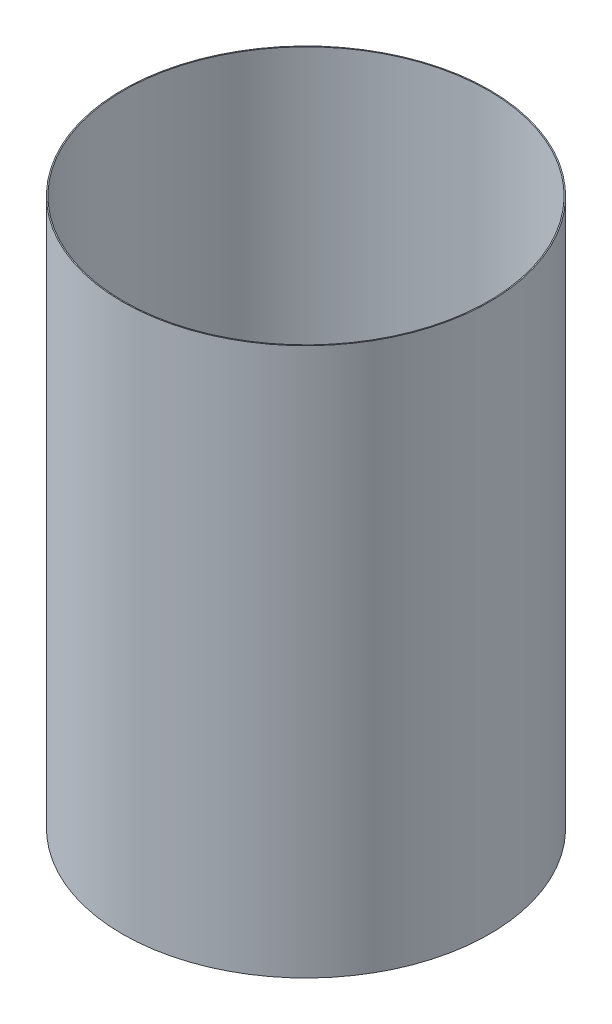
SolidWorks part; units mm, degrees
material "Thornel Mat VMA"
ref_plane "Front Plane" through (0, 0, 0) normal (0, 0, 1) x (1, 0, 0)
ref_plane "Top Plane" through (0, 0, 0) normal (0, 1, 0) x (1, 0, 0)
ref_plane "Right Plane" through (0, 0, 0) normal (1, 0, 0) x (0, 0, -1)
ref_axis "Axis1" through (0, 55, 0) along (0, -1, 0)
sketch "Sketch1" plane through (0, 0, 0) normal (0, 0, 1) x (1, 0, 0)
  line L0 (-44.45, -69.0032) -> (-44.45, -202.3532)
  line L2 (-38.1, -202.3532) -> (0, -202.3532) construction
  line L3 (-38.1, -69.0032) -> (0, -69.0032) construction
revolve "Revolve-Thin1" add sketch "Sketch1" angle 360 about axis through (0, 55, 0) along (0, -1, 0)
equation "\"D3@Revolve-Thin1\"=\"CF THICKNESS@Cryo Tank.Assembly\""
